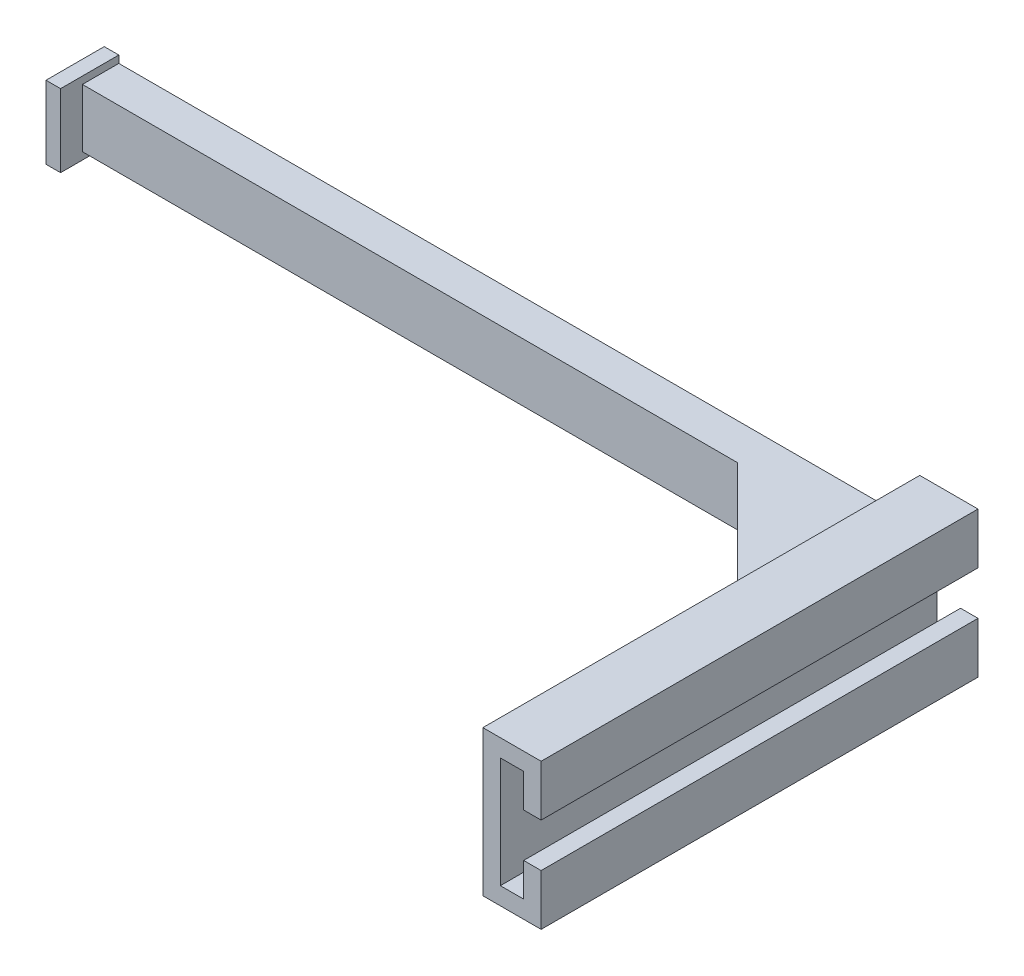
SolidWorks part; units mm, degrees
material "ABS"
ref_plane "前视基准面" through (0, 0, 0) normal (0, 0, 1) x (1, 0, 0)
ref_plane "上视基准面" through (0, 0, 0) normal (0, 1, 0) x (1, 0, 0)
ref_plane "右视基准面" through (0, 0, 0) normal (1, 0, 0) x (0, 0, -1)
sketch "草图1" plane through (0, 0, 0) normal (0, 0, 1) x (1, 0, 0)
  line L5 (5.6, 10.6) -> (3.2, 10.6)
  line L6 (0, 0) -> (3.2, 0)
  line L11 (0, 0) -> (0, 15.2)
  line L12 (0, 15.2) -> (3.2, 15.2)
  line L17 (3.2, 0) -> (3.2, 4.6)
  line L18 (-2.4, -2.4) -> (5.6, -2.4)
  line L21 (-2.4, -2.4) -> (-2.4, 17.6)
  line L22 (-2.4, 17.6) -> (5.6, 17.6)
  line L23 (5.6, -2.4) -> (5.6, 4.6)
  line L24 (3.2, 4.6) -> (5.6, 4.6)
  line L25 (3.2, 10.6) -> (3.2, 15.2)
  line L26 (5.6, 10.6) -> (5.6, 17.6)
  point P5 (1.6, 17.6)
  point P9 (1.6, 15.2)
  dimension "D1" = 3.2
  dimension "D2" = 15.2
  dimension "D3" = 8
  dimension "D4" = 20
  dimension "D5" = 0
extrude "凸台-拉伸1" add sketch "草图1" along normal blind 60 contours L12 L25 L5 L26 L22 L21 L18 L23 L24 L17 L6 L11
sketch "草图2" plane through (-2.4, 0, 0) normal (-1, 0, 0) x (0, 0, 1)
  line L0 (0, -2.4) -> (0, 17.6) construction
  line L1 (0, 11.6) -> (5, 11.6)
  line L2 (0, 11.6) -> (0, 3.6)
  line L3 (0, 3.6) -> (5, 3.6)
  line L4 (5, 11.6) -> (5, 3.6)
  line L5 (60, 17.6) -> (0, 17.6) construction
  line L6 (60, -2.4) -> (0, -2.4) construction
  dimension "D1" = 6
  dimension "D2" = 6
  dimension "D3" = 5
extrude "凸台-拉伸2" add sketch "草图2" along normal blind 197 contours L4 L3 L2 L1
chamfer "倒角1" distance 20 angle 45 1 edges at (-2.4, 7.6, 5)
chamfer "倒角2" distance 2 angle 45 2 edges at (-2.4, 3.6, 12.5) (-2.4, 11.6, 12.5)
sketch "草图4" plane through (0, 0, 0) normal (0, 0, -1) x (-1, 0, 0)
  line L0 (199.4, 3.6) -> (4.4, 3.6) construction
  line L1 (199.4, 11.6) -> (114.4, 11.6)
  line L2 (199.4, 11.6) -> (199.4, 3.6)
  line L3 (199.4, 3.6) -> (114.4, 3.6)
  line L4 (114.4, 11.6) -> (114.4, 3.6)
  dimension "D1" = 85
extrude "切除-拉伸1" cut sketch "草图4" against normal blind 10
sketch "草图5" plane through (-114.4, 0, 0) normal (-1, 0, 0) x (0, 0, 1)
  line L0 (0, 11.6) -> (0, 13.6) construction
  line L1 (0, 12.6) -> (8, 12.6)
  line L2 (0, 12.6) -> (0, 2.6)
  line L3 (0, 2.6) -> (8, 2.6)
  line L4 (8, 12.6) -> (8, 2.6)
  line L6 (5, 3.6) -> (5, 11.6) construction
  dimension "D1" = 3
extrude "凸台-拉伸3" add sketch "草图5" against normal blind 2
equation "\"60、\"=50"
